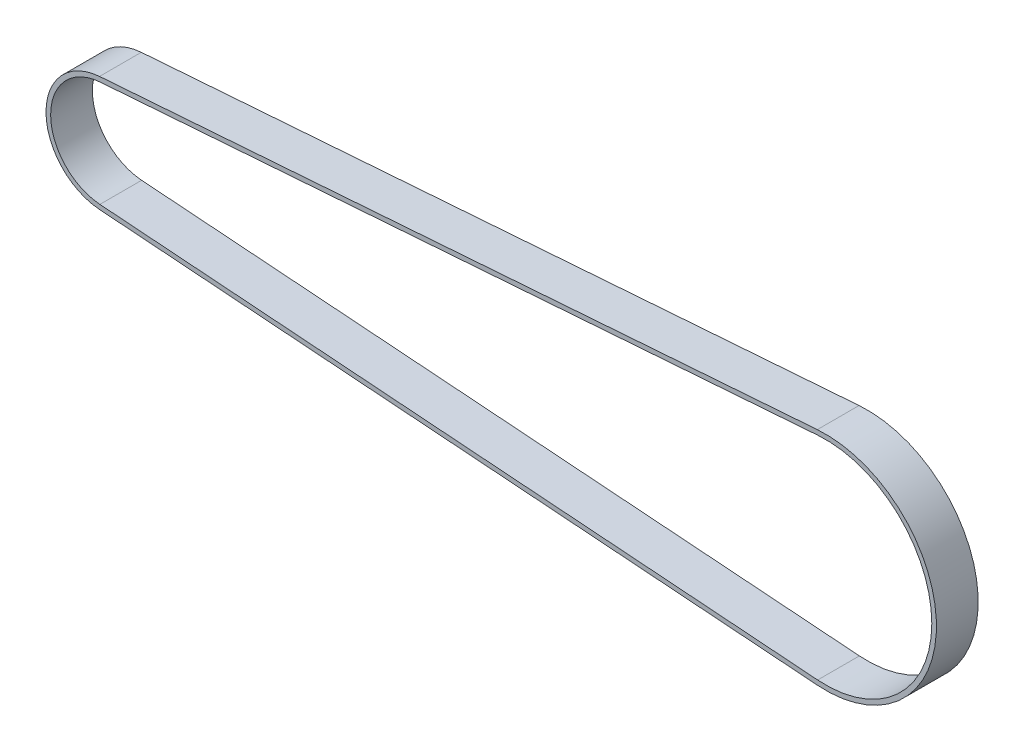
SolidWorks part; units mm, degrees
material "SBR"
ref_plane "Front Plane" through (0, 0, 0) normal (0, 0, 1) x (1, 0, 0)
ref_plane "Top Plane" through (0, 0, 0) normal (0, 1, 0) x (1, 0, 0)
ref_plane "Right Plane" through (0, 0, 0) normal (1, 0, 0) x (0, 0, -1)
sketch "Sketch1" plane through (0, 0, 0) normal (0, 0, 1) x (1, 0, 0)
  line L0 (-78.6329, 11.428) -> (76.1008, 22.8561) construction
  line L1 (76.1008, -22.8561) -> (-78.6329, -11.428) construction
  line L2 (-77.7889, 0) -> (77.7889, 0) construction
  line L3 (76.0272, -23.8533) -> (-78.7066, -12.4253)
  line L4 (-78.7066, 12.4253) -> (76.0272, 23.8533)
  line L5 (76.1008, -22.8561) -> (-78.6329, -11.428)
  line L6 (-78.6329, 11.428) -> (76.1008, 22.8561)
  arc A0 (-78.6329, 11.428) -> (-78.6329, -11.428) centre (-77.7889, 0) ccw construction
  arc A1 (76.1008, -22.8561) -> (76.1008, 22.8561) centre (77.7889, 0) ccw construction
  arc A2 (-78.7066, 12.4253) -> (-78.7066, -12.4253) centre (-77.7889, 0) ccw
  arc A3 (76.0272, -23.8533) -> (76.0272, 23.8533) centre (77.7889, 0) ccw
  arc A4 (-78.6329, 11.428) -> (-78.6329, -11.428) centre (-77.7889, 0) ccw
  arc A5 (76.1008, -22.8561) -> (76.1008, 22.8561) centre (77.7889, 0) ccw
  point P3 (0, 0)
  dimension "D1" = 45.8366
  dimension "D2" = 22.9183
  dimension "D3" = 155.5778
  dimension "D4" = 420
  dimension "D5" = 1
  dimension "D6" = 0
extrude "Boss-Extrude2" add sketch "Sketch1" along normal blind 9
